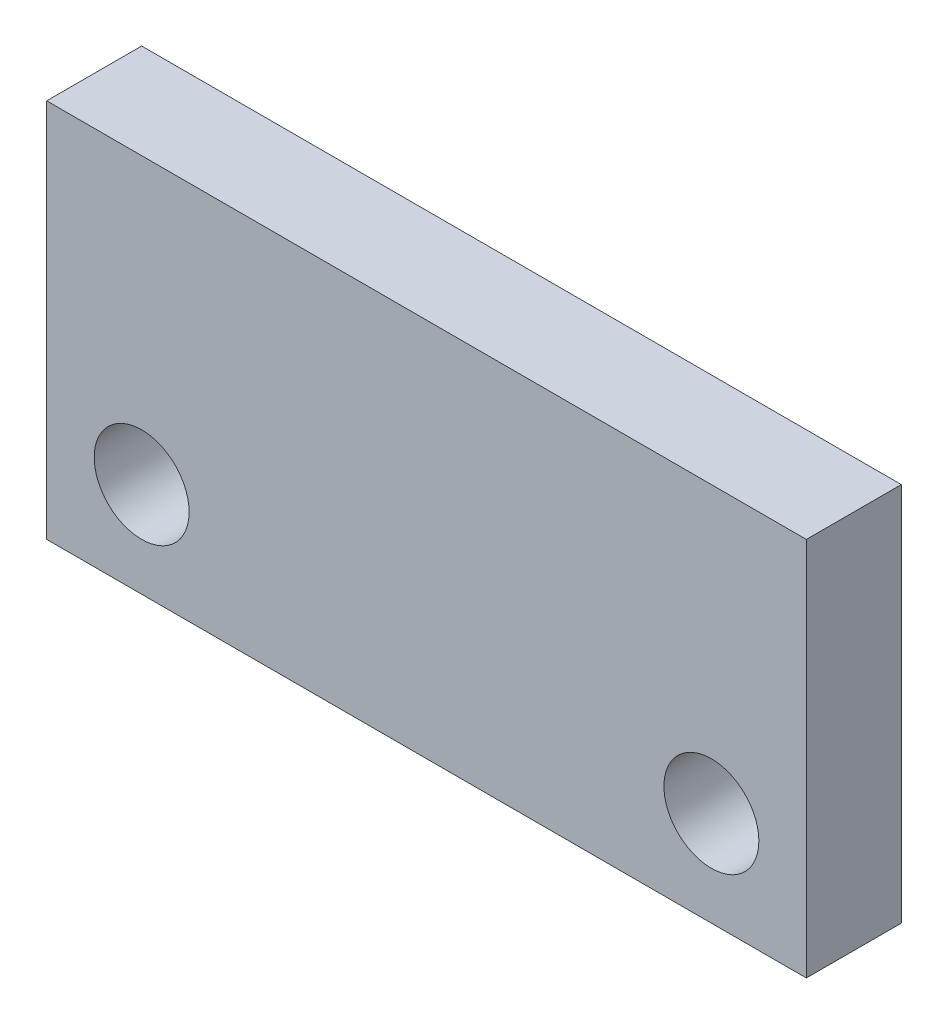
SolidWorks part; units mm, degrees
material "AISI 1020"
ref_plane "Front Plane" through (0, 0, 0) normal (0, 0, 1) x (1, 0, 0)
ref_plane "Top Plane" through (0, 0, 0) normal (0, 1, 0) x (1, 0, 0)
ref_plane "Right Plane" through (0, 0, 0) normal (1, 0, 0) x (0, 0, -1)
sketch "Sketch1" plane through (0, 0, 0) normal (0, 0, 1) x (1, 0, 0)
  line L0 (0, 6.35) -> (50.8, 6.35) construction
  line L1 (0, 0) -> (50.8, 0)
  line L2 (0, 0) -> (0, 25.4)
  line L3 (0, 25.4) -> (50.8, 25.4)
  line L4 (50.8, 0) -> (50.8, 25.4)
  circle A2 centre (6.35, 6.35) radius 3.175
  circle A3 centre (44.45, 6.35) radius 3.175
  point P11 (0, 0)
  point P12 (0, 0)
  dimension "D3" = 6.35
  dimension "D4" = 6.35
  dimension "D1" = 50.8
  dimension "D2" = 25.4
  dimension "D5" = 38.1
  dimension "D6" = 6.35
  dimension "D7" = 19.05
extrude "Boss-Extrude1" add sketch "Sketch1" along normal blind 6.35
